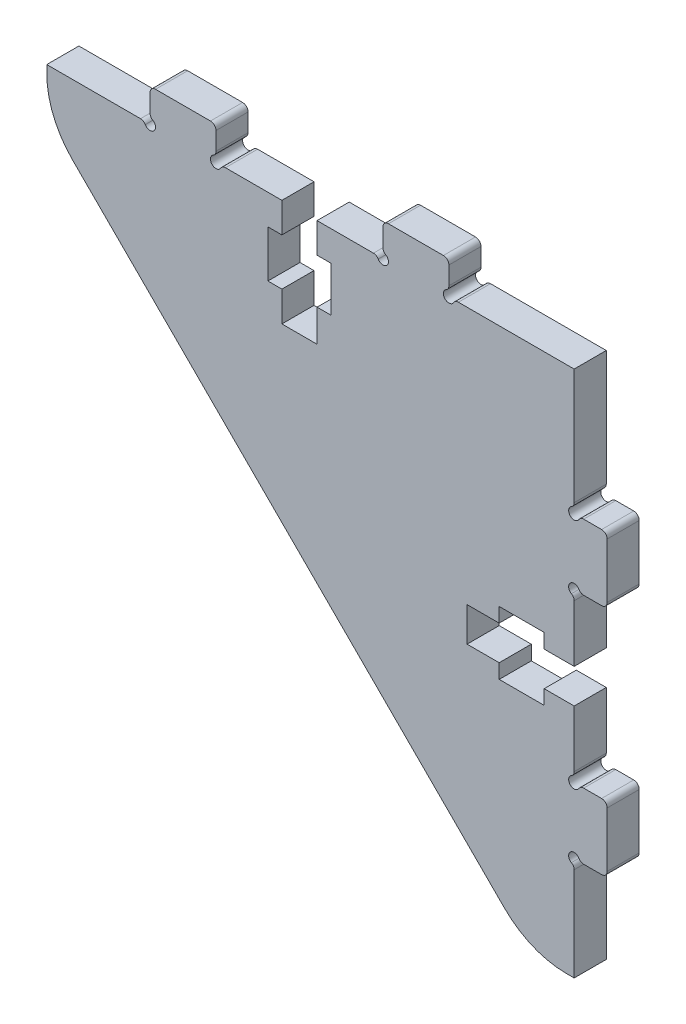
SolidWorks part; units mm, degrees
material "Plain Carbon Steel"
ref_plane "Front Plane" through (0, 0, 0) normal (0, 0, 1) x (1, 0, 0)
ref_plane "Top Plane" through (0, 0, 0) normal (0, 1, 0) x (1, 0, 0)
ref_plane "Right Plane" through (0, 0, 0) normal (1, 0, 0) x (0, 0, -1)
sketch "Sketch1" plane through (0, 0, 0) normal (0, 0, 1) x (1, 0, 0)
  line L0 (278.7489, 1025.6817) -> (277.0723, 1025.6817)
  line L1 (279.262, 1020.0383) -> (279.262, 1025.1687)
  line L2 (277.0723, 1019.5252) -> (278.7489, 1019.5252)
  line L3 (276.1837, 1009.88) -> (276.1837, 1018.6366)
  line L4 (275.4795, 1009.88) -> (276.1837, 1009.88)
  line L5 (229.3358, 1052.6236) -> (269.6751, 1012.2843)
  line L6 (226.9315, 1059.1322) -> (226.9315, 1058.428)
  line L7 (235.6881, 1059.1322) -> (226.9315, 1059.1322)
  line L8 (236.5767, 1061.6974) -> (236.5767, 1060.0208)
  line L9 (242.2202, 1062.2105) -> (237.0898, 1062.2105)
  line L10 (242.7332, 1060.0208) -> (242.7332, 1061.6974)
  line L11 (248.8898, 1059.1322) -> (243.6219, 1059.1322)
  line L12 (248.8898, 1056.3322) -> (248.8898, 1059.1322)
  line L13 (247.5815, 1056.3322) -> (248.8898, 1056.3322)
  line L14 (247.5815, 1051.9496) -> (247.5815, 1056.3322)
  line L15 (248.8898, 1051.9496) -> (247.5815, 1051.9496)
  line L16 (248.8898, 1049.1322) -> (248.8898, 1051.9496)
  line L17 (252.1732, 1049.1322) -> (248.8898, 1049.1322)
  line L18 (252.1732, 1052.1322) -> (252.1732, 1049.1322)
  line L19 (253.4815, 1052.1322) -> (252.1732, 1052.1322)
  line L20 (252.1732, 1056.3322) -> (253.4815, 1056.3322)
  line L21 (252.1732, 1059.1322) -> (252.1732, 1056.3322)
  line L22 (257.4411, 1059.1322) -> (252.1732, 1059.1322)
  line L23 (258.3298, 1061.6975) -> (258.3298, 1060.0208)
  line L24 (263.9732, 1062.2105) -> (258.8428, 1062.2105)
  line L25 (264.4863, 1060.0208) -> (264.4863, 1061.6975)
  line L26 (276.1837, 1059.1322) -> (265.3749, 1059.1322)
  line L27 (276.1837, 1048.3234) -> (276.1837, 1059.1322)
  line L28 (278.7489, 1047.4348) -> (277.0723, 1047.4348)
  line L29 (279.262, 1041.7913) -> (279.262, 1046.9217)
  line L30 (277.0723, 1041.2783) -> (278.7489, 1041.2783)
  line L31 (266.1837, 1035.08) -> (269.1837, 1035.08)
  line L32 (266.1837, 1031.88) -> (266.1837, 1035.08)
  line L33 (269.1837, 1031.88) -> (266.1837, 1031.88)
  line L34 (269.1837, 1030.53) -> (269.1837, 1031.88)
  line L35 (273.3837, 1030.53) -> (269.1837, 1030.53)
  line L36 (273.3837, 1031.88) -> (273.3837, 1030.53)
  line L37 (276.1837, 1031.88) -> (273.3837, 1031.88)
  line L38 (276.1837, 1026.5704) -> (276.1837, 1031.88)
  line L39 (276.1837, 1035.08) -> (276.1837, 1040.3896)
  line L40 (273.3837, 1035.08) -> (276.1837, 1035.08)
  line L41 (273.3837, 1036.43) -> (273.3837, 1035.08)
  line L42 (269.1837, 1036.43) -> (273.3837, 1036.43)
  line L43 (269.1837, 1035.08) -> (269.1837, 1036.43)
  line L44 (253.4815, 1056.3322) -> (253.4815, 1052.1322)
  line L45 (276.1837, 1059.1322) -> (281.6055, 1059.1322) construction
  line L46 (276.1837, 59.1322) -> (276.1837, 50059.1322) construction
  line L47 (276.1837, 67.5691) -> (276.1837, 50067.5691) construction
  line L48 (251.1837, 59.1322) -> (251.1837, 50059.1322) construction
  line L49 (276.1837, 1034.1322) -> (281.6055, 1034.1322) construction
  arc A0 (275.9271, 1026.1261) -> (276.1837, 1026.5704) centre (275.6706, 1026.5704) ccw
  arc A1 (275.9271, 1026.1261) -> (276.628, 1025.4252) centre (276.1837, 1025.6817) ccw
  arc A2 (277.0723, 1025.6817) -> (276.628, 1025.4252) centre (277.0723, 1025.1687) ccw
  arc A3 (279.262, 1025.1687) -> (278.7489, 1025.6817) centre (278.7489, 1025.1687) ccw
  arc A4 (278.7489, 1019.5252) -> (279.262, 1020.0383) centre (278.7489, 1020.0383) ccw
  arc A5 (276.628, 1019.7817) -> (277.0723, 1019.5252) centre (277.0723, 1020.0383) ccw
  arc A6 (276.628, 1019.7817) -> (275.9271, 1019.0809) centre (276.1837, 1019.5252) ccw
  arc A7 (276.1837, 1018.6366) -> (275.9271, 1019.0809) centre (275.6706, 1018.6366) ccw
  arc A8 (269.6751, 1012.2843) -> (275.4795, 1009.88) centre (275.4795, 1018.0887) ccw
  arc A9 (226.9315, 1058.428) -> (229.3358, 1052.6236) centre (235.1402, 1058.428) ccw
  arc A10 (236.1324, 1058.8757) -> (235.6881, 1059.1322) centre (235.6881, 1058.6191) ccw
  arc A11 (236.1324, 1058.8757) -> (236.8332, 1059.5765) centre (236.5767, 1059.1322) ccw
  arc A12 (236.5767, 1060.0208) -> (236.8332, 1059.5765) centre (237.0898, 1060.0208) ccw
  arc A13 (237.0898, 1062.2105) -> (236.5767, 1061.6974) centre (237.0898, 1061.6974) ccw
  arc A14 (242.7332, 1061.6974) -> (242.2202, 1062.2105) centre (242.2202, 1061.6974) ccw
  arc A15 (242.4767, 1059.5765) -> (242.7332, 1060.0208) centre (242.2202, 1060.0208) ccw
  arc A16 (242.4767, 1059.5765) -> (243.1775, 1058.8757) centre (242.7332, 1059.1322) ccw
  arc A17 (243.6219, 1059.1322) -> (243.1775, 1058.8757) centre (243.6219, 1058.6191) ccw
  arc A18 (257.8855, 1058.8757) -> (257.4411, 1059.1322) centre (257.4411, 1058.6191) ccw
  arc A19 (257.8855, 1058.8757) -> (258.5863, 1059.5765) centre (258.3298, 1059.1322) ccw
  arc A20 (258.3298, 1060.0208) -> (258.5863, 1059.5765) centre (258.8428, 1060.0208) ccw
  arc A21 (258.8428, 1062.2105) -> (258.3298, 1061.6975) centre (258.8428, 1061.6975) ccw
  arc A22 (264.4863, 1061.6975) -> (263.9732, 1062.2105) centre (263.9732, 1061.6975) ccw
  arc A23 (264.2298, 1059.5765) -> (264.4863, 1060.0208) centre (263.9732, 1060.0208) ccw
  arc A24 (264.2298, 1059.5765) -> (264.9306, 1058.8757) centre (264.4863, 1059.1322) ccw
  arc A25 (265.3749, 1059.1322) -> (264.9306, 1058.8757) centre (265.3749, 1058.6191) ccw
  arc A26 (275.9271, 1047.8791) -> (276.1837, 1048.3234) centre (275.6706, 1048.3234) ccw
  arc A27 (275.9271, 1047.8791) -> (276.628, 1047.1783) centre (276.1837, 1047.4348) ccw
  arc A28 (277.0723, 1047.4348) -> (276.628, 1047.1783) centre (277.0723, 1046.9217) ccw
  arc A29 (279.262, 1046.9217) -> (278.7489, 1047.4348) centre (278.7489, 1046.9217) ccw
  arc A30 (278.7489, 1041.2783) -> (279.262, 1041.7913) centre (278.7489, 1041.7913) ccw
  arc A31 (276.628, 1041.5348) -> (277.0723, 1041.2783) centre (277.0723, 1041.7913) ccw
  arc A32 (276.628, 1041.5348) -> (275.9271, 1040.834) centre (276.1837, 1041.2783) ccw
  arc A33 (276.1837, 1040.3896) -> (275.9271, 1040.834) centre (275.6706, 1040.3896) ccw
  dimension "D1" = 25
  dimension "D2" = 25
extrude "Boss-Extrude1" add sketch "Sketch1" along normal blind 3
